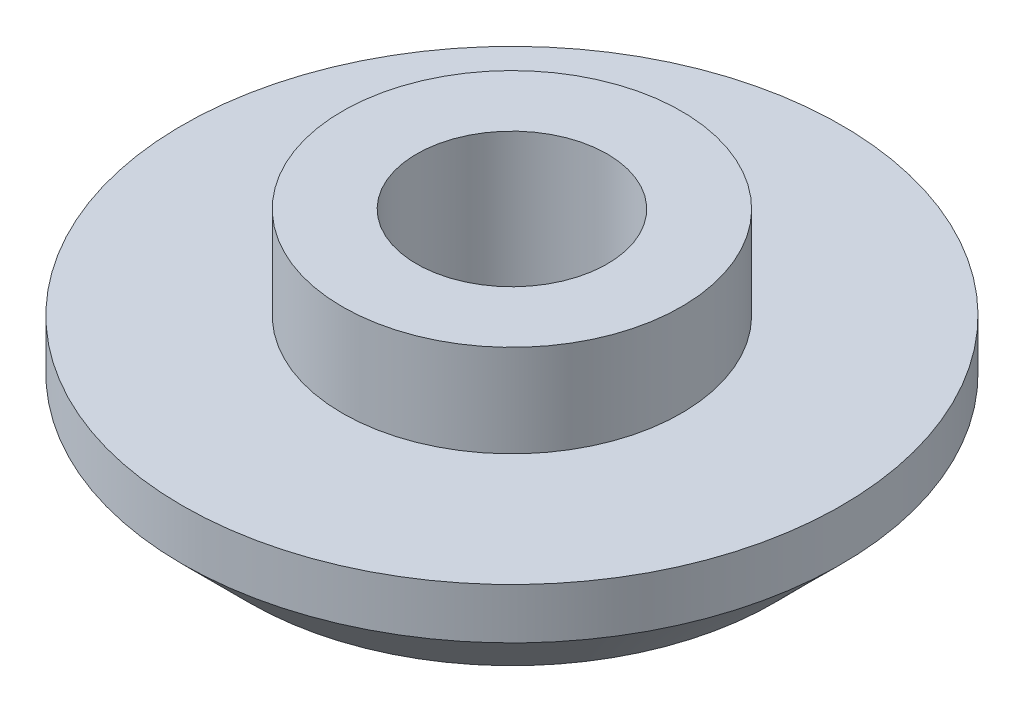
SolidWorks part; units mm, degrees
ref_plane "Front Plane" through (0, 0, 0) normal (0, 0, 1) x (1, 0, 0)
ref_plane "Top Plane" through (0, 0, 0) normal (0, 1, 0) x (1, 0, 0)
ref_plane "Right Plane" through (0, 0, 0) normal (1, 0, 0) x (0, 0, -1)
sketch "Sketch1" plane through (0, 0, 0) normal (0, 0, 1) x (1, 0, 0)
  line L0 (0, 0) -> (3.5, 0) construction
  line L1 (0, 1.7014) -> (4.1104, 1.7014) construction
  line L2 (0, 0.6) -> (3.5, 0.6)
  line L3 (3.5, 0.6) -> (3.5, 0)
  line L4 (0, 4.41) -> (3.556, 4.41)
  line L5 (3.5, 0) -> (5.5, 0)
  line L6 (5.5, 0) -> (6.9142, 1.4142)
  line L7 (6.9142, 1.4142) -> (6.9142, 2.4754)
  line L8 (0, 4.41) -> (0, 0.6)
  line L9 (3.556, 4.41) -> (3.556, 2.4754)
  line L10 (3.556, 2.4754) -> (6.9142, 2.4754)
  dimension "D1" = 3.5
  dimension "D2" = 0.6
  dimension "D3" = 3.556
  dimension "D4" = 135
  dimension "D5" = 3.81
  dimension "D6" = 2
revolve "Revolve1" add sketch "Sketch1" angle 360 about L8
sketch "Sketch2" plane through (0, 0.6, 0) normal (0, -1, 0) x (1, 0, 0)
  circle A0 centre (0, 0) radius 2
  dimension "D1" = 4
extrude "Cut-Extrude1" cut sketch "Sketch2" against normal through all
